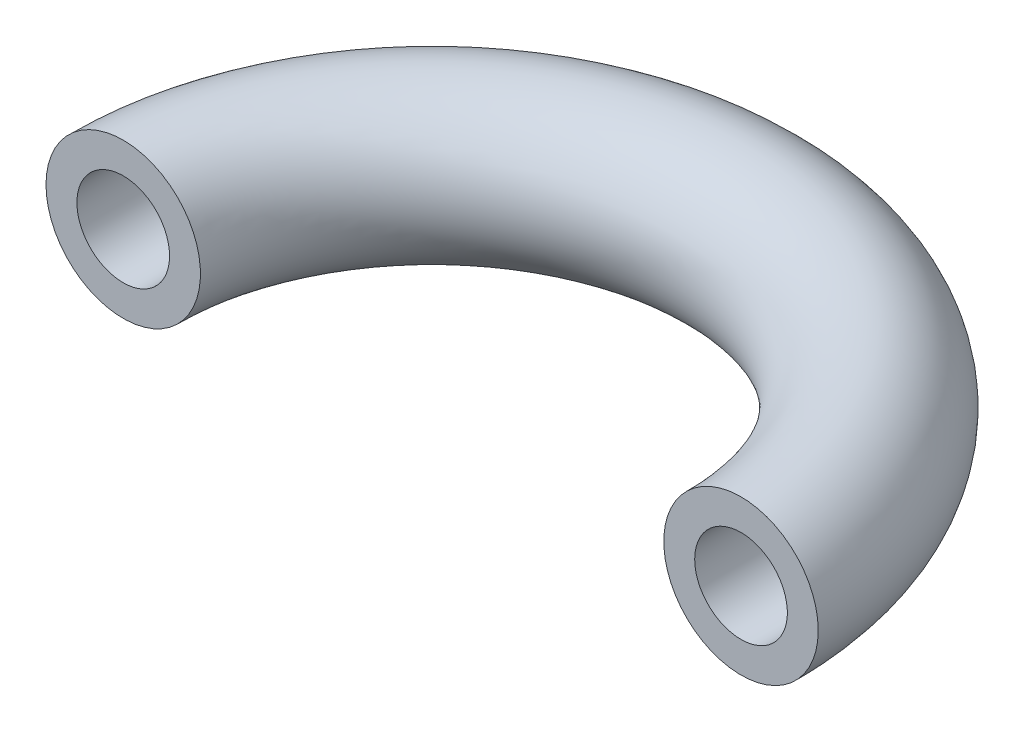
SolidWorks part; units mm, degrees
material "Cast Alloy Steel"
ref_plane "Front Plane" through (0, 0, 0) normal (0, 0, 1) x (1, 0, 0)
ref_plane "Top Plane" through (0, 0, 0) normal (0, 1, 0) x (1, 0, 0)
ref_plane "Right Plane" through (0, 0, 0) normal (1, 0, 0) x (0, 0, -1)
sketch "Sketch1" plane through (0, 0, 0) normal (0, 1, 0) x (1, 0, 0)
  arc A0 (-10, 0) -> (10, 0) centre (0, 0) cw
  dimension "D1" = 10
sweep "Sweep1" add path "Sketch1" circular profile diameter 5 parameters "D3"=5
sketch "Sketch14" plane through (0, 0, 0) normal (0, 0, 1) x (1, 0, 0)
  circle A0 centre (-10, 0) radius 1.5
  dimension "D1" = 3
extrude "Cut-Extrude1" cut sketch "Sketch14" against normal blind 4
mirror "Mirror1" about plane through (0, 0, 0) normal (1, 0, 0) of "Cut-Extrude1"
